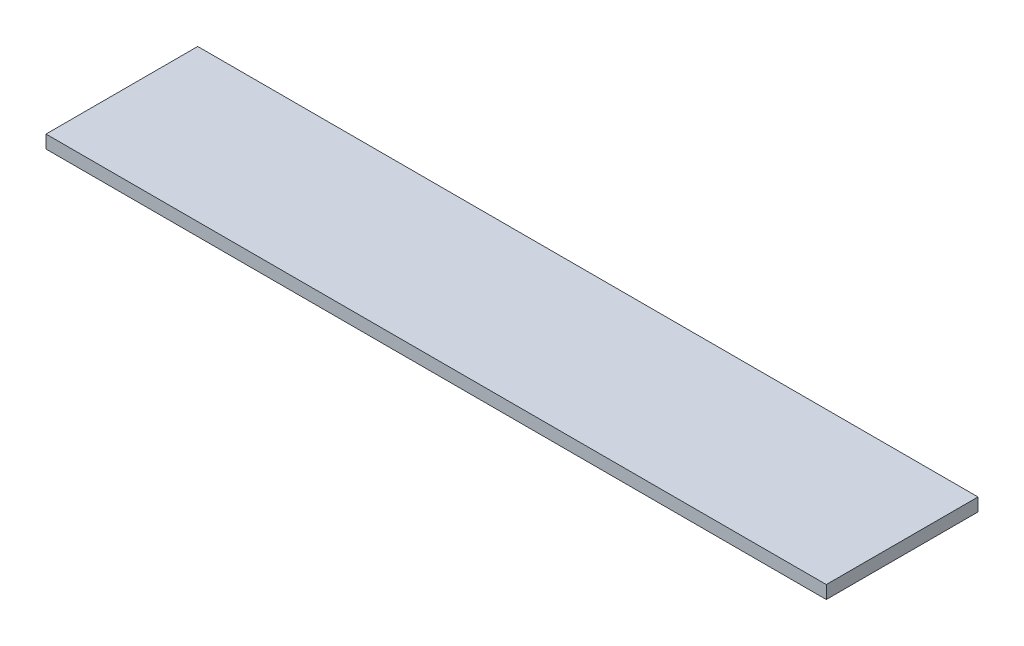
SolidWorks part; units mm, degrees
ref_plane "Front Plane" through (0, 0, 0) normal (0, 0, 1) x (1, 0, 0)
ref_plane "Top Plane" through (0, 0, 0) normal (0, 1, 0) x (1, 0, 0)
ref_plane "Right Plane" through (0, 0, 0) normal (1, 0, 0) x (0, 0, -1)
sketch "Sketch1" plane through (0, 0, 0) normal (0, 1, 0) x (1, 0, 0)
  line L1 (-104.6869, 23.6057) -> (75.3131, 23.6057)
  line L2 (-104.6869, 23.6057) -> (-104.6869, 58.6057)
  line L3 (-104.6869, 58.6057) -> (75.3131, 58.6057)
  line L4 (75.3131, 23.6057) -> (75.3131, 58.6057)
  dimension "D1" = 180
  dimension "D2" = 35
extrude "Boss-Extrude1" add sketch "Sketch1" along normal blind 3
